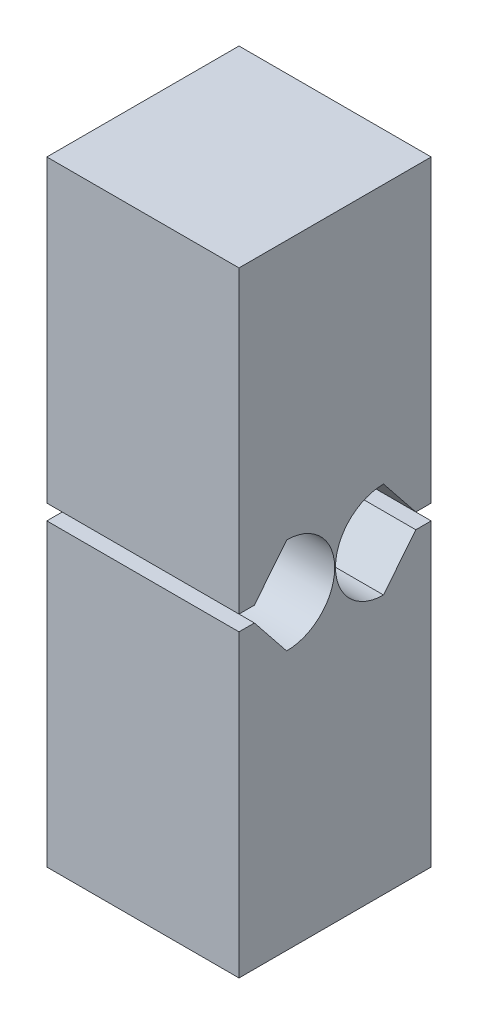
SolidWorks part; units mm, degrees
material "Beryllium Copper, UNS C17200"
ref_plane "Front Plane" through (0, 0, 0) normal (0, 0, 1) x (1, 0, 0)
ref_plane "Top Plane" through (0, 0, 0) normal (0, 1, 0) x (1, 0, 0)
ref_plane "Right Plane" through (0, 0, 0) normal (1, 0, 0) x (0, 0, -1)
sketch "Sketch1" plane through (0, 0, 0) normal (0, 1, 0) x (1, 0, 0)
  line L1 (-3.175, 3.175) -> (3.175, 3.175)
  line L2 (-3.175, 3.175) -> (-3.175, -3.175)
  line L3 (-3.175, -3.175) -> (3.175, -3.175)
  line L4 (3.175, 3.175) -> (3.175, -3.175)
  dimension "D1" = 3.175
  dimension "D2" = 3.175
  dimension "D3" = 3.175
  dimension "D4" = 3.175
extrude "Boss-Extrude1" add sketch "Sketch1" along normal mid plane 20.32
sketch "Sketch2" plane through (3.175, 0, 0) normal (1, 0, 0) x (0, 0, -1)
  line L0 (-3.175, 0.254) -> (-3.175, -0.254)
  line L1 (-3.175, 10.16) -> (-3.175, -10.16) construction
  line L2 (-3.175, -0.254) -> (-2.667, -0.254)
  line L3 (-2.667, -0.254) -> (-1.6002, -1.5875)
  line L4 (-3.175, 0.254) -> (-2.667, 0.254)
  line L5 (-2.667, 0.254) -> (-1.6002, 1.5875)
  arc A0 (-1.6002, 1.5875) -> (-1.6002, -1.5875) centre (-1.6002, 0) cw
  dimension "D1" = 0.254
  dimension "D2" = 0.254
  dimension "D3" = 0.508
  dimension "D4" = 0.508
extrude "Cut-Extrude1" cut sketch "Sketch2" against normal up to next (6.35 mm away)
mirror "Mirror1" about plane through (0, 0, 0) normal (0, 0, 1) of "Cut-Extrude1"
